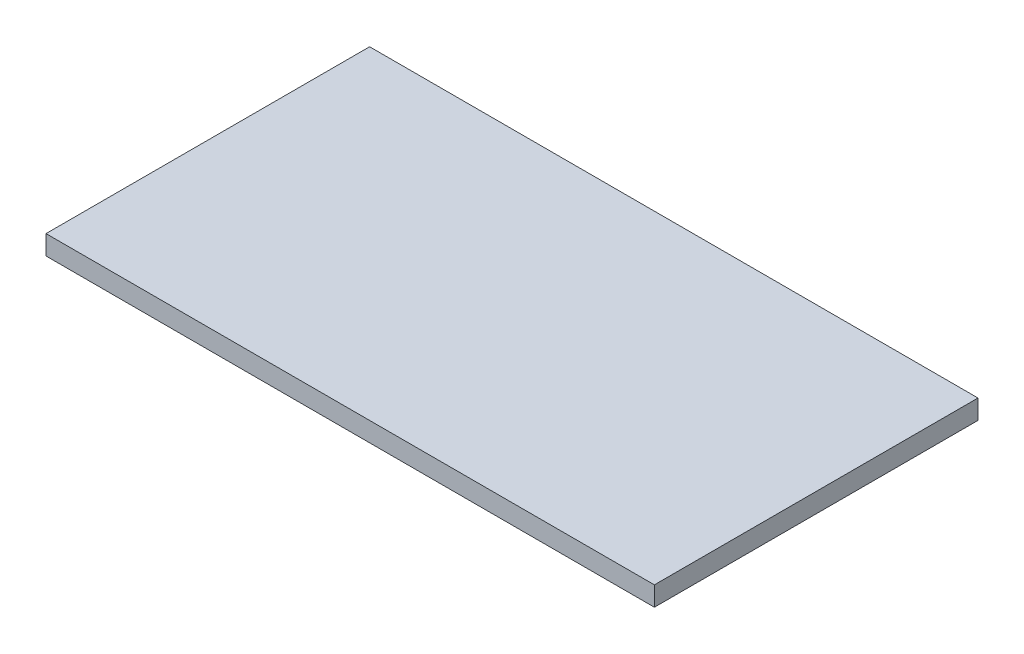
SolidWorks part; units mm, degrees
ref_plane "Front Plane" through (0, 0, 0) normal (0, 0, 1) x (1, 0, 0)
ref_plane "Top Plane" through (0, 0, 0) normal (0, 1, 0) x (1, 0, 0)
ref_plane "Right Plane" through (0, 0, 0) normal (1, 0, 0) x (0, 0, -1)
sketch "Sketch1" plane through (0, 0, 0) normal (0, 1, 0) x (1, 0, 0)
  line L1 (282, -150) -> (-282, -150)
  line L2 (282, -150) -> (282, 150)
  line L3 (282, 150) -> (-282, 150)
  line L4 (-282, -150) -> (-282, 150)
  line L5 (282, -150) -> (-282, 150) construction
  line L6 (282, 150) -> (-282, -150) construction
  point P0 (0, 0)
  dimension "D1" = 300
  dimension "D2" = 564
extrude "Boss-Extrude1" add sketch "Sketch1" along normal blind 18
equation "\"H_DSP\"=18"
equation "\"D1@Boss-Extrude1\"=\"H_DSP\""
